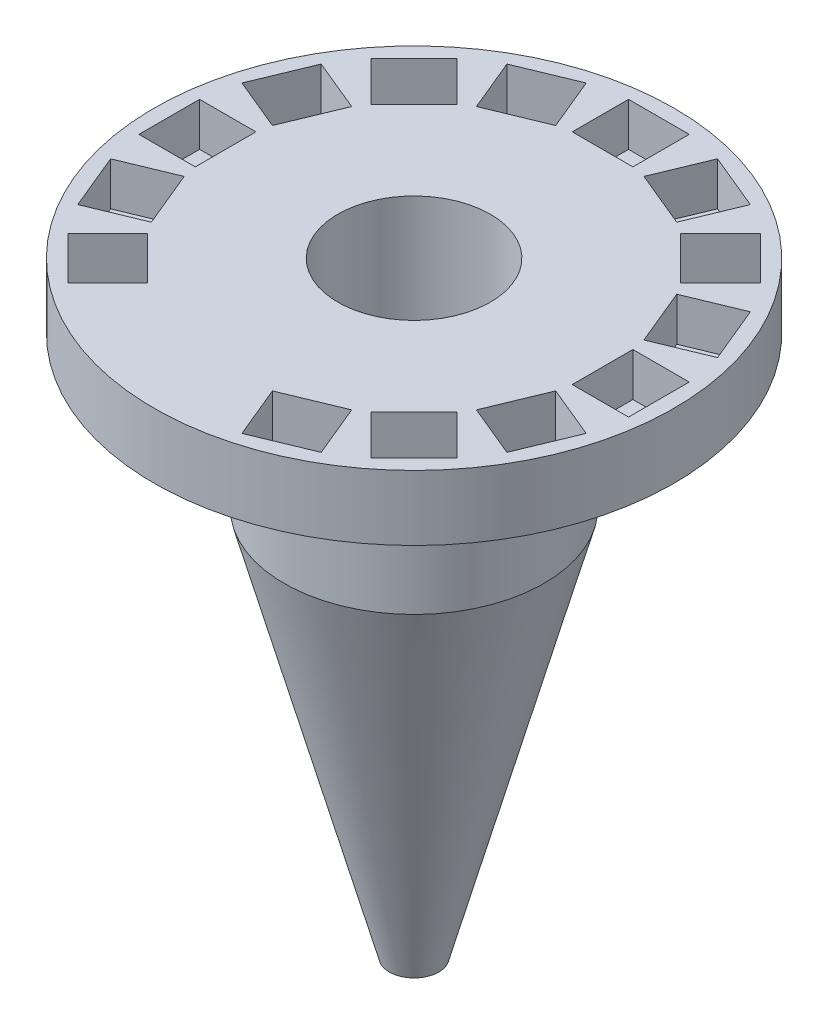
SolidWorks part; units mm, degrees
ref_plane "Front Plane" through (0, 0, 0) normal (0, 0, 1) x (1, 0, 0)
ref_plane "Top Plane" through (0, 0, 0) normal (0, 1, 0) x (1, 0, 0)
ref_plane "Right Plane" through (0, 0, 0) normal (1, 0, 0) x (0, 0, -1)
sketch "Sketch1" plane through (0, 0, 0) normal (1, 0, 0) x (0, 0, -1)
  line L0 (0, 0) -> (0, 8288.9361) construction
  line L1 (1.76, 2.5) -> (6, 2.5)
  line L2 (6, 2.5) -> (6, 1)
  line L3 (6, 1) -> (3, 1)
  line L4 (3, 1) -> (3, -2.5)
  line L6 (1.76, -2.5) -> (1.76, 2.5)
  line L7 (1.76, -2.5) -> (0.2957, -11.4829)
  line L8 (0.2957, -11.4829) -> (0.5705, -11.4829)
  line L9 (0.5705, -11.4829) -> (3, -2.5)
  point P5 (1.76, 0)
  dimension "D1" = 1.76
  dimension "D2" = 6
  dimension "D3" = 1.5
  dimension "D4" = 5
  dimension "D5" = 3
revolve "Revolve1" add sketch "Sketch1" angle 360 about L0
sketch "Sketch2" plane through (0, 2.5, 0) normal (0, 1, 0) x (1, 0, 0)
  line L1 (-0.7, 4.35) -> (0.7, 4.35)
  line L2 (-0.7, 4.35) -> (-0.7, 5.65)
  line L3 (-0.7, 5.65) -> (0.7, 5.65)
  line L4 (0.7, 4.35) -> (0.7, 5.65)
  line L5 (-0.7, 4.35) -> (0.7, 5.65) construction
  line L6 (-0.7, 5.65) -> (0.7, 4.35) construction
  point P0 (0, 5)
  point P5 (0, 0)
  dimension "D1" = 1.4
  dimension "D2" = 1.3
  dimension "D3" = 5
extrude "Cut-Extrude1" cut sketch "Sketch2" against normal blind 1
pattern_circular "CirPattern1" count 16 over 360 about axis through (0, 0, 0) along (0, 1, 0) skipping 8, 9 of "Cut-Extrude1"
equation "\"Radius\"= 5"
equation "\"D3@Sketch2\"=\"Radius\""
